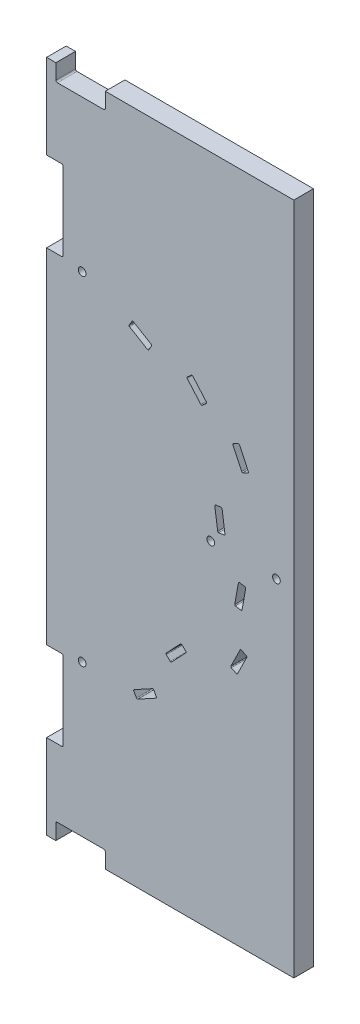
SolidWorks part; units mm, degrees
ref_plane "Front Plane" through (0, 0, 0) normal (0, 0, 1) x (1, 0, 0)
ref_plane "Top Plane" through (0, 0, 0) normal (0, 1, 0) x (1, 0, 0)
ref_plane "Right Plane" through (0, 0, 0) normal (1, 0, 0) x (0, 0, -1)
sketch "Sketch1" plane through (0, 0, 0) normal (0, 0, 1) x (1, 0, 0)
  line L0 (154.1815, -104.8875) -> (-5.8185, -104.8875) construction
  line L1 (-5.8185, -104.8875) -> (154.1815, -104.8875)
  line L2 (-5.8185, -104.8875) -> (-5.8185, 331.1125)
  line L3 (-5.8185, 331.1125) -> (154.1815, 331.1125)
  line L4 (154.1815, -104.8875) -> (154.1815, 331.1125)
  line L5 (154.1815, 331.1125) -> (154.1815, -104.8875) construction
  line L6 (-5.8185, -104.8875) -> (-5.8185, 331.1125) construction
  line L7 (-5.8185, 331.1125) -> (154.1815, 331.1125) construction
extrude "Boss-Extrude1" add sketch "Sketch1" along normal blind 12.7
sketch "Sketch3" plane through (0, 0, 0) normal (0, 0, -1) x (-1, 0, 0)
  line L21 (-59.4682, 200.0397) -> (-47.8784, 206.9626)
  line L22 (-62.1289, 203.324) -> (-60.291, 200.2471)
  line L23 (-50.3317, 211.0697) -> (-61.9215, 204.1468)
  line L24 (-47.671, 207.7854) -> (-49.5089, 210.8623)
  line L25 (-59.4682, 200.0397) -> (-47.8784, 206.9626)
  line L26 (-62.1289, 203.324) -> (-60.291, 200.2471)
  line L27 (-50.3317, 211.0697) -> (-61.9215, 204.1468)
  line L28 (-47.671, 207.7854) -> (-49.5089, 210.8623)
  line L54 (-94.0415, 186.4866) -> (-85.1659, 196.6588)
  line L55 (-97.5886, 188.7853) -> (-94.8881, 186.429)
  line L56 (-88.7707, 199.8041) -> (-97.6463, 189.6319)
  line L57 (-85.2236, 197.5054) -> (-87.9241, 199.8617)
  line L58 (-94.0415, 186.4866) -> (-85.1659, 196.6588)
  line L59 (-97.5886, 188.7853) -> (-94.8881, 186.429)
  line L60 (-88.7707, 199.8041) -> (-97.6463, 189.6319)
  line L61 (-85.2236, 197.5054) -> (-87.9241, 199.8617)
  arc A24 (-60.291, 200.2471) -> (-59.4682, 200.0397) centre (-59.7759, 200.5548) ccw
  arc A25 (-61.9215, 204.1468) -> (-62.1289, 203.324) centre (-61.6138, 203.6317) ccw
  arc A26 (-49.5089, 210.8623) -> (-50.3317, 211.0697) centre (-50.024, 210.5546) ccw
  arc A27 (-47.8784, 206.9626) -> (-47.671, 207.7854) centre (-48.1861, 207.4777) ccw
  arc A28 (-60.291, 200.2471) -> (-59.4682, 200.0397) centre (-59.7759, 200.5548) ccw
  arc A29 (-61.9215, 204.1468) -> (-62.1289, 203.324) centre (-61.6138, 203.6317) ccw
  arc A30 (-49.5089, 210.8623) -> (-50.3317, 211.0697) centre (-50.024, 210.5546) ccw
  arc A31 (-47.8784, 206.9626) -> (-47.671, 207.7854) centre (-48.1861, 207.4777) ccw
  arc A64 (-94.8881, 186.429) -> (-94.0415, 186.4866) centre (-94.4936, 186.8811) ccw
  arc A65 (-97.6463, 189.6319) -> (-97.5886, 188.7853) centre (-97.1942, 189.2374) ccw
  arc A66 (-87.9241, 199.8617) -> (-88.7707, 199.8041) centre (-88.3186, 199.4096) ccw
  arc A67 (-85.1659, 196.6588) -> (-85.2236, 197.5054) centre (-85.618, 197.0533) ccw
  arc A68 (-94.8881, 186.429) -> (-94.0415, 186.4866) centre (-94.4936, 186.8811) ccw
  arc A69 (-97.6463, 189.6319) -> (-97.5886, 188.7853) centre (-97.1942, 189.2374) ccw
  arc A70 (-87.9241, 199.8617) -> (-88.7707, 199.8041) centre (-88.3186, 199.4096) ccw
  arc A71 (-85.1659, 196.6588) -> (-85.2236, 197.5054) centre (-85.618, 197.0533) ccw
  dimension "D1" = 0.1
  dimension "D2" = 0.1
extrude "Cut-Extrude1" cut sketch "Sketch3" against normal through all
pattern_circular "CirPattern1" count 3 every 51.26 about axis through (-0.3185, 113.1125, 0) along (0, 0, 1) of "Cut-Extrude1"
sketch "Sketch4" plane through (0, 0, 0) normal (0, 0, -1) x (-1, 0, 0)
  line L24 (-124.5077, 163.3373) -> (-121.2608, 161.8198)
  line L25 (-119.0814, 176.3651) -> (-124.7972, 164.1349)
  line L26 (-115.0368, 175.1372) -> (-118.2838, 176.6547)
  line L27 (-120.4632, 162.1094) -> (-114.7473, 174.3396)
  line L28 (-124.5077, 163.3373) -> (-121.2608, 161.8198)
  line L29 (-119.0814, 176.3651) -> (-124.7972, 164.1349)
  line L30 (-115.0368, 175.1372) -> (-118.2838, 176.6547)
  line L31 (-120.4632, 162.1094) -> (-114.7473, 174.3396)
  arc A20 (-121.2608, 161.8198) -> (-120.4632, 162.1094) centre (-121.0067, 162.3634) ccw
  arc A21 (-124.7972, 164.1349) -> (-124.5077, 163.3373) centre (-124.2536, 163.8808) ccw
  arc A22 (-118.2838, 176.6547) -> (-119.0814, 176.3651) centre (-118.5378, 176.1111) ccw
  arc A23 (-114.7473, 174.3396) -> (-115.0368, 175.1372) centre (-115.2909, 174.5937) ccw
  arc A24 (-121.2608, 161.8198) -> (-120.4632, 162.1094) centre (-121.0067, 162.3634) ccw
  arc A25 (-124.7972, 164.1349) -> (-124.5077, 163.3373) centre (-124.2536, 163.8808) ccw
  arc A26 (-118.2838, 176.6547) -> (-119.0814, 176.3651) centre (-118.5378, 176.1111) ccw
  arc A27 (-114.7473, 174.3396) -> (-115.0368, 175.1372) centre (-115.2909, 174.5937) ccw
  dimension "D1" = 0.1
extrude "Cut-Extrude2" cut sketch "Sketch4" against normal through all
pattern_circular "CirPattern2" count 2 every 51.26 about axis through (-0.3185, 113.1125, 0) along (0, 0, 1) of "Cut-Extrude2"
hole_wizard "Ø5.0 (5) Diameter Hole1" positions "Sketch8" profile "Sketch7" hole size "Ø5.0" standard "Ansi Metric" end condition through all
sketch "Sketch8" plane through (0, 0, 0) normal (0, 0, -1) x (-1, 0, 0)
  circle A0 centre (-142.9315, 113.1125) radius 2 construction
  point P0 (-142.9315, 113.1125)
sketch "Sketch7" plane through (142.9315, 113.1125, 0) normal (1, 0, 0) x (0, 1, 0)
  line L0 (0, 0) -> (0, 12.7)
  line L1 (0, 12.7) -> (2.5, 12.7)
  line L2 (2.5, 12.7) -> (2.5, 0)
  line L5 (2.5, 0) -> (0, 0)
  line L11 (0, -6.35) -> (0, 107.95) construction
  dimension "Thru Hole Dia." = 5
  dimension "Thru Hole Depth" = 12.7
sketch "Sketch11" plane through (0, 0, 12.7) normal (0, 0, 1) x (1, 0, 0)
  point P7 (142.9315, 113.1125)
  point P9 (100.4315, 113.1125)
  point P13 (17.1815, 222.4711)
  point P18 (17.1815, 3.7538)
pattern_sketch "Sketch-Pattern9" of "Ø5.0 (5) Diameter Hole1" driven by "Sketch11"
sketch "Sketch9" plane through (0, 0, 0) normal (0, 0, -1) x (-1, 0, 0)
  line L0 (5.8185, 331.1125) -> (5.8185, -104.8875) construction
  line L1 (5.8185, 276.3625) -> (-3.9315, 276.3625)
  line L2 (5.8185, 276.3625) -> (5.8185, 224.3625)
  line L3 (5.8185, 224.3625) -> (-3.9315, 224.3625)
  line L4 (-4.9315, 275.3625) -> (-4.9315, 225.3625)
  line L5 (-154.1815, 331.1125) -> (5.8185, 331.1125) construction
  line L6 (-32.1815, 331.1125) -> (-0.1815, 331.1125)
  line L7 (-32.1815, 331.1125) -> (-32.1815, 321.3625)
  line L8 (-31.1815, 320.3625) -> (-1.1815, 320.3625)
  line L9 (-0.1815, 331.1125) -> (-0.1815, 321.3625)
  line L10 (-31.1815, 321.1125) -> (-1.1815, 321.1125) construction
  line L11 (-4.1815, 275.3625) -> (-4.1815, 225.3625) construction
  line L12 (-4.1815, 225.3625) -> (6.0185, 225.3625) construction
  line L13 (6.0185, 275.3625) -> (-4.1815, 275.3625) construction
  line L14 (-1.1815, 321.1125) -> (-1.1815, 331.3125) construction
  line L15 (-31.1815, 331.3125) -> (-31.1815, 321.1125) construction
  arc A0 (-3.9315, 224.3625) -> (-4.9315, 225.3625) centre (-3.9315, 225.3625) cw
  arc A1 (-4.9315, 275.3625) -> (-3.9315, 276.3625) centre (-3.9315, 275.3625) cw
  arc A2 (-1.1815, 320.3625) -> (-0.1815, 321.3625) centre (-1.1815, 321.3625) ccw
  arc A3 (-31.1815, 320.3625) -> (-32.1815, 321.3625) centre (-31.1815, 321.3625) cw
  dimension "D7" = 1
  dimension "D1" = 0.75
  dimension "D2" = 0.75
  dimension "D3" = 1
  dimension "D4" = 1
  dimension "D5" = 1
  dimension "D6" = 1
extrude "Cut-Extrude3" cut sketch "Sketch9" against normal through all
ref_plane "Plane1" through (0, 113.1125, 0) normal (0, 1, 0) x (-1, 0, 0)
mirror "Mirror1" about plane through (0, 113.1125, 0) normal (0, 1, 0) of "Cut-Extrude3"
